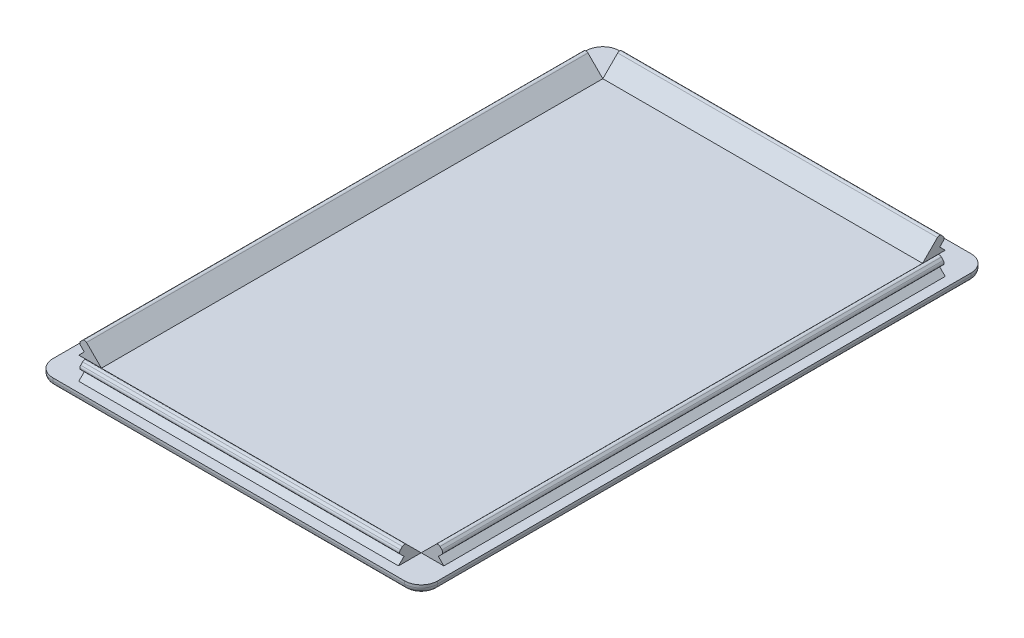
SolidWorks part; units mm, degrees
ref_plane "Front Plane" through (0, 0, 0) normal (0, 0, 1) x (1, 0, 0)
ref_plane "Top Plane" through (0, 0, 0) normal (0, 1, 0) x (1, 0, 0)
ref_plane "Right Plane" through (0, 0, 0) normal (1, 0, 0) x (0, 0, -1)
sketch "EDIT GLOBAL VARIABLE WITH PCB DIMENSIONS" plane through (0, 0, 0) normal (0, 1, 0) x (1, 0, 0)
  line L1 (-34.98, -51.49) -> (34.98, -51.49)
  line L2 (-34.98, -51.49) -> (-34.98, 51.49)
  line L3 (-34.98, 51.49) -> (34.98, 51.49)
  line L4 (34.98, -51.49) -> (34.98, 51.49)
  line L5 (-34.98, -51.49) -> (34.98, 51.49) construction
  line L6 (-34.98, 51.49) -> (34.98, -51.49) construction
  line L7 (-30.48, -46.99) -> (30.48, -46.99) construction
  line L8 (-30.48, -46.99) -> (-30.48, 46.99) construction
  line L9 (-30.48, 46.99) -> (30.48, 46.99) construction
  line L10 (30.48, -46.99) -> (30.48, 46.99) construction
  line L11 (-30.48, -46.99) -> (30.48, 46.99) construction
  line L12 (-30.48, 46.99) -> (30.48, -46.99) construction
  point P0 (0, 0)
  point P6 (0, 0)
  dimension "D3" = 4.5
  dimension "D4" = 4.5
  dimension "D2" = 93.98
  dimension "D17" = 60.96
extrude "Boss-Extrude1" add sketch "EDIT GLOBAL VARIABLE WITH PCB DIMENSIONS" along normal blind 1.5
fillet "Fillet1" radius 3 4 edges at (-34.98, 0.75, -51.49) (34.98, 0.75, -51.49) (34.98, 0.75, 51.49) (-34.98, 0.75, 51.49)
ref_plane "Plane1" through (-33.18, 0, 0) normal (-1, 0, 0) x (0, 0, 1)
ref_plane "Plane2" through (0, 0, 49.69) normal (0, 0, 1) x (1, 0, 0)
ref_plane "Plane3" through (33.18, 0, 0) normal (1, 0, 0) x (0, 0, -1)
ref_plane "Plane4" through (0, 0, -49.69) normal (0, 0, -1) x (-1, 0, 0)
ref_plane "Plane5" through (0, 0, -45.5687) normal (0, 0, -1) x (-1, 0, 0)
ref_plane "Plane6" through (-29.0587, 0, 0) normal (-1, 0, 0) x (0, 0, 1)
ref_plane "Plane7" through (0, 0, 45.5687) normal (0, 0, 1) x (1, 0, 0)
ref_plane "Plane8" through (29.0587, 0, 0) normal (1, 0, 0) x (0, 0, -1)
sketch "Sketch2" plane through (0, 0, 45.5687) normal (0, 0, 1) x (1, 0, 0)
  line L9 (33.18, 1.5) -> (29.0587, 1.5)
  line L11 (34.98, 1.5) -> (31.98, 1.5) construction
  line L12 (-31.98, 1.5) -> (31.98, 1.5) construction
  line L13 (29.0587, 1.5) -> (32.1193, 4.5607)
  line L14 (32.1193, 4.5607) -> (33.18, 3.5)
  line L15 (33.18, 3.5) -> (32.18, 2.5)
  line L16 (32.18, 2.5) -> (33.18, 1.5)
  line L17 (34.98, 1.5) -> (34.98, 0) construction
  line L18 (33.18, 3.5) -> (33.18, 1.5) construction
  dimension "D1" = 2
  dimension "D2" = 90
  dimension "D3" = 45
  dimension "D4" = 1.5
  dimension "D5" = 1.8
extrude "Boss-Extrude2" add sketch "Sketch2" against normal up to surface (91.1374 mm away) up to plane "Plane5"
sketch "Sketch3" plane through (0, 0, 45.5687) normal (0, 0, 1) x (1, 0, 0)
  line L9 (-33.18, 1.5) -> (-29.0587, 1.5)
  line L11 (-31.98, 1.5) -> (-34.98, 1.5) construction
  line L12 (-31.98, 1.5) -> (31.98, 1.5) construction
  line L13 (-29.0587, 1.5) -> (-32.1193, 4.5607)
  line L14 (-32.1193, 4.5607) -> (-33.18, 3.5)
  line L15 (-33.18, 3.5) -> (-32.18, 2.5)
  line L16 (-32.18, 2.5) -> (-33.18, 1.5)
  line L17 (-34.98, 0) -> (-34.98, 1.5) construction
  line L18 (-33.18, 3.5) -> (-33.18, 1.5) construction
  dimension "D1" = 45
  dimension "D2" = 90
  dimension "D3" = 1.5
  dimension "D4" = 2
  dimension "D5" = 1.8
extrude "Boss-Extrude3" add sketch "Sketch3" against normal up to surface (91.1374 mm away) up to plane "Plane5"
sketch "Sketch4" plane through (-29.0587, 0, 0) normal (-1, 0, 0) x (0, 0, 1)
  line L9 (-49.69, 1.5) -> (-45.5687, 1.5)
  line L12 (-48.49, 1.5) -> (-51.49, 1.5) construction
  line L13 (-48.49, 1.5) -> (48.49, 1.5) construction
  line L14 (-45.5687, 1.5) -> (-48.6293, 4.5607)
  line L15 (-48.6293, 4.5607) -> (-49.69, 3.5)
  line L16 (-49.69, 3.5) -> (-48.69, 2.5)
  line L17 (-48.69, 2.5) -> (-49.69, 1.5)
  line L18 (-51.49, 0) -> (-51.49, 1.5) construction
  dimension "D1" = 45
  dimension "D2" = 90
  dimension "D3" = 1.5
  dimension "D4" = 2
  dimension "D5" = 1.8
  dimension "D6" = 1.8
extrude "Boss-Extrude4" add sketch "Sketch4" against normal up to surface (58.1174 mm away) up to plane "Plane8"
sketch "Sketch5" plane through (-29.0587, 0, 0) normal (-1, 0, 0) x (0, 0, 1)
  line L0 (45.5687, 1.5) -> (49.69, 1.5)
  line L1 (-48.49, 1.5) -> (48.49, 1.5) construction
  line L2 (51.49, 1.5) -> (48.49, 1.5) construction
  line L3 (49.69, 1.5) -> (48.69, 2.5)
  line L4 (48.69, 2.5) -> (49.69, 3.5)
  line L5 (49.69, 3.5) -> (48.6293, 4.5607)
  line L6 (48.6293, 4.5607) -> (45.5687, 1.5)
  line L7 (51.49, 1.5) -> (51.49, 0) construction
  dimension "D1" = 45
  dimension "D2" = 90
  dimension "D3" = 1.5
  dimension "D4" = 90
  dimension "D5" = 1.8
  dimension "D6" = 1.8
  dimension "D7" = 2
extrude "Boss-Extrude5" add sketch "Sketch5" against normal up to surface (58.1174 mm away) up to plane "Plane8"
fillet "Fillet2" radius 0.5 8 edges at (0, 3.5, 49.69) (0, 4.5607, 48.6293) (-33.18, 3.5, 0) (-32.1193, 4.5607, 0) (0, 3.5, -49.69) (0, 4.5607, -48.6293) (33.18, 3.5, 0) (32.1193, 4.5607, 0)
fillet "Fillet3" radius 1 8 edges at (-34.1013, 0, -50.6113) (-34.98, 0, 0) (-34.1013, 0, 50.6113) (0, 0, 51.49) (34.1013, 0, 50.6113) (0, 0, -51.49) (34.1013, 0, -50.6113) (34.98, 0, 0)
equation "\"LENGTH\"= 3.7in\t\t\t'longest of two dimensions of pcb"
equation "\"WIDTH\"= 2.4in\t\t\t'shortest of two dimensions of pcb"
equation "\"D2@EDIT GLOBAL VARIABLE WITH PCB DIMENSIONS\" = \"LENGTH\""
equation "\"D17@EDIT GLOBAL VARIABLE WITH PCB DIMENSIONS\" = \"WIDTH\""
equation "\"HOLE_DIA\"= 0.1in\t\t'mounting hole diameter"
equation "\"HOLE_DIST\"= .1375069in\t\t'distance to mount hole centerline from edge of PCB"
equation "\"PCB_THICK\"= 0.063in\t\t'nominal thickness of PCB, usually 1.6mm"
equation "\"TOP_CLEAR\"= 1in\t\t'Clearance above top of PCB, tallest component plus desired clearance"
equation "\"BOTTOM_CLEAR\"= 4mm\t\t'Clearance below bottom of PCB, minimum 4mm"
